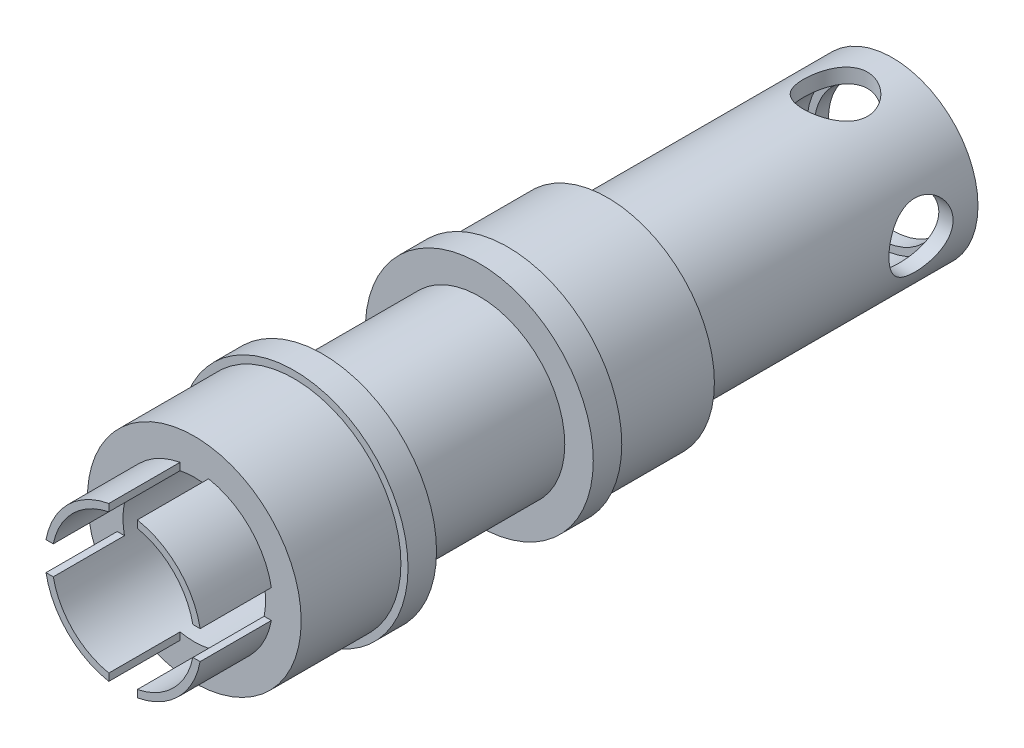
SolidWorks part; units mm, degrees
material "Alliage 1060"
ref_plane "Plan de face" through (0, 0, 0) normal (0, 0, 1) x (1, 0, 0)
ref_plane "Plan de dessus" through (0, 0, 0) normal (0, 1, 0) x (1, 0, 0)
ref_plane "Plan de droite" through (0, 0, 0) normal (1, 0, 0) x (0, 0, -1)
sketch "Esquisse1" plane through (0, 0, 0) normal (0, 0, 1) x (1, 0, 0)
  circle A0 centre (0, 0) radius 5
  circle A1 centre (0, 0) radius 6
  dimension "D1" = 10
  dimension "D2" = 12
extrude "Boss.-Extru.1" add sketch "Esquisse1" along normal blind 20
sketch "Esquisse2" plane through (0, 0, 0) normal (0, 0, -1) x (-1, 0, 0)
  circle A0 centre (0, 0) radius 4.5
  circle A1 centre (0, 0) radius 6
  dimension "D1" = 12
  dimension "D2" = 9
extrude "Boss.-Extru.2" add sketch "Esquisse2" against normal blind 1
sketch "Esquisse3" plane through (0, 0, 20) normal (0, 0, 1) x (1, 0, 0)
  circle A0 centre (0, 0) radius 7.5
  circle A1 centre (0, 0) radius 5
  dimension "D1" = 10
  dimension "D2" = 15
extrude "Boss.-Extru.3" add sketch "Esquisse3" along normal blind 7
sketch "Esquisse4" plane through (0, 0, 27) normal (0, 0, 1) x (1, 0, 0)
  circle A0 centre (0, 0) radius 5
  circle A1 centre (0, 0) radius 8
  dimension "D1" = 10
  dimension "D2" = 16
extrude "Boss.-Extru.4" add sketch "Esquisse4" along normal blind 2
sketch "Esquisse7" plane through (0, 0, 29) normal (0, 0, 1) x (1, 0, 0)
  circle A0 centre (0, 0) radius 5
  circle A1 centre (0, 0) radius 6
  dimension "D1" = 10
  dimension "D2" = 12
extrude "Boss.-Extru.7" add sketch "Esquisse7" along normal blind 11
sketch "Esquisse8" plane through (0, 0, 40) normal (0, 0, 1) x (1, 0, 0)
  circle A0 centre (0, 0) radius 5
  circle A1 centre (0, 0) radius 8
  dimension "D1" = 10
  dimension "D2" = 16
extrude "Boss.-Extru.8" add sketch "Esquisse8" along normal blind 2
hole_wizard "Dégagement M41" positions "Esquisse3D6" profile "Esquisse14" hole size "M4" standard "ISO" end condition through all
sketch3d "Esquisse3D6"
  point P0 (6, 0, 4)
  point P2 (0, 6, 4)
  dimension "D1" = 4
  dimension "D2" = 4
sketch "Esquisse14" plane through (6, 0, 4) normal (0, 1, 0) x (0, 0, -1)
  line L0 (0, 0) -> (0, 14)
  line L1 (0, 14) -> (2.25, 14)
  line L2 (2.25, 14) -> (2.25, 0)
  line L5 (2.25, 0) -> (0, 0)
  line L11 (0, -6.35) -> (0, 107.95) construction
  dimension "Diamètre du perçage jusqu'au prochain" = 4.5
  dimension "Profondeur du perçage jusqu'au prochain" = 14
sketch "Esquisse15" plane through (0, 0, 42) normal (0, 0, 1) x (1, 0, 0)
  circle A0 centre (0, 0) radius 5
  circle A1 centre (0, 0) radius 7.5
  dimension "D1" = 10
  dimension "D2" = 15
extrude "Boss.-Extru.9" add sketch "Esquisse15" along normal blind 7
sketch "Esquisse16" plane through (0, 0, 49) normal (0, 0, 1) x (1, 0, 0)
  circle A0 centre (0, 0) radius 5
  circle A1 centre (0, 0) radius 5.5
  dimension "D1" = 10
  dimension "D2" = 11
extrude "Boss.-Extru.10" add sketch "Esquisse16" along normal blind 5
sketch "Esquisse17" plane through (0, 0, 54) normal (0, 0, 1) x (1, 0, 0)
  line L1 (-10, 1) -> (10, 1)
  line L2 (-10, 1) -> (-10, -1)
  line L3 (-10, -1) -> (10, -1)
  line L4 (10, 1) -> (10, -1)
  line L5 (-1, -10) -> (1, -10)
  line L6 (-1, -10) -> (-1, 10)
  line L7 (-1, 10) -> (1, 10)
  line L8 (1, -10) -> (1, 10)
  dimension "D1" = 2
  dimension "D2" = 1
  dimension "D3" = 10
  dimension "D4" = 20
  dimension "D5" = 2
  dimension "D6" = 20
  dimension "D7" = 10
  dimension "D8" = 1
extrude "Enlèv. mat.-Extru.1" cut sketch "Esquisse17" against normal blind 5 contours L6 L7 L8 L5 | L1 L4 L3 L2
